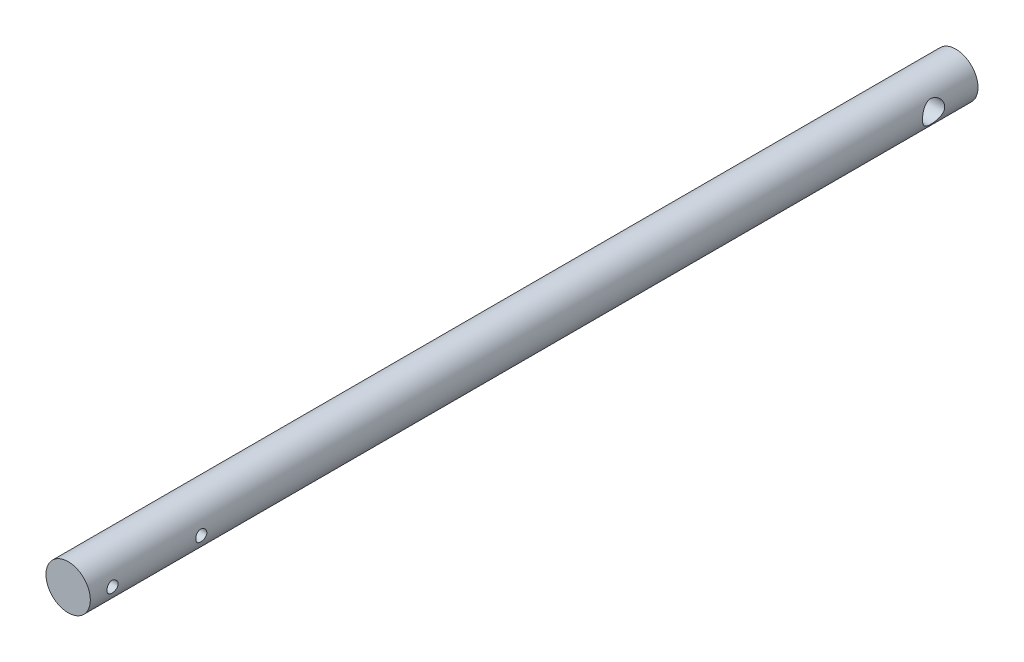
SolidWorks part; units mm, degrees
material "6061-T6 (SS)"
ref_plane "Front Plane" through (0, 0, 0) normal (0, 0, 1) x (1, 0, 0)
ref_plane "Top Plane" through (0, 0, 0) normal (0, 1, 0) x (1, 0, 0)
ref_plane "Right Plane" through (0, 0, 0) normal (1, 0, 0) x (0, 0, -1)
sketch "Sketch1" plane through (0, 0, 0) normal (0, 0, 1) x (1, 0, 0)
  circle A0 centre (0, 0) radius 12.7
  dimension "D1" = 25.4
extrude "Boss-Extrude1" add sketch "Sketch1" along normal mid plane 508
sketch "Sketch2" plane through (0, 0, 0) normal (1, 0, 0) x (0, 0, -1)
  line L0 (-254, 12.7) -> (-254, -12.7) construction
  line L1 (254, -12.7) -> (254, 12.7) construction
  circle A0 centre (-241.3, 0) radius 3.175
  circle A1 centre (-190.5, 0) radius 3.175
  circle A2 centre (228.6, 0) radius 6.35
  point P8 (0, 0)
  dimension "D1" = 6.35
  dimension "D2" = 12.7
  dimension "D5" = 25.4
  dimension "D3" = 12.7
  dimension "D4" = 50.8
extrude "Cut-Extrude1" cut sketch "Sketch2" against normal through all both and the other way through all
